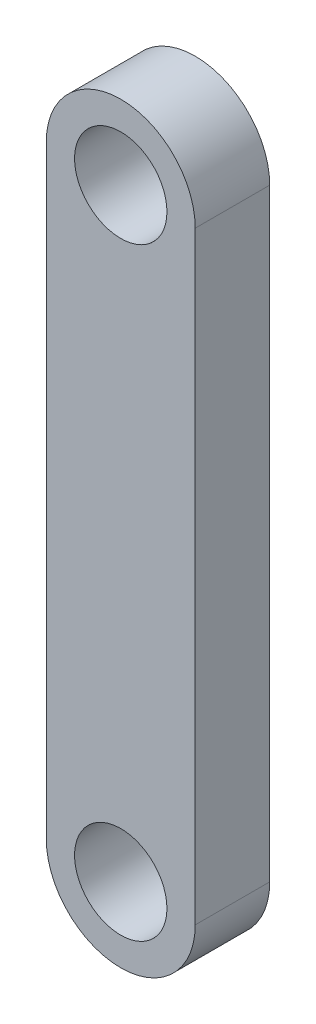
SolidWorks part; units mm, degrees
ref_plane "Front Plane" through (0, 0, 0) normal (0, 0, 1) x (1, 0, 0)
ref_plane "Top Plane" through (0, 0, 0) normal (0, 1, 0) x (1, 0, 0)
ref_plane "Right Plane" through (0, 0, 0) normal (1, 0, 0) x (0, 0, -1)
sketch "Sketch1" plane through (0, 0, 0) normal (0, 0, 1) x (1, 0, 0)
  line L0 (0, 38.075) -> (0, -13.36) construction
  line L1 (6.35, 38.075) -> (6.35, -13.36)
  line L2 (-6.35, 38.075) -> (-6.35, -13.36)
  arc A0 (6.35, 38.075) -> (-6.35, 38.075) centre (0, 38.075) ccw
  arc A1 (-6.35, -13.36) -> (6.35, -13.36) centre (0, -13.36) ccw
  circle A2 centre (0, 38.075) radius 3.937
  circle A3 centre (0, -13.36) radius 3.937
  point P3 (0, 12.3575)
  dimension "D1" = 7.874
  dimension "D2" = 7.874
  dimension "D3" = 51.435
  dimension "D4" = 12.7
extrude "Boss-Extrude1" add sketch "Sketch1" along normal blind 6.35
